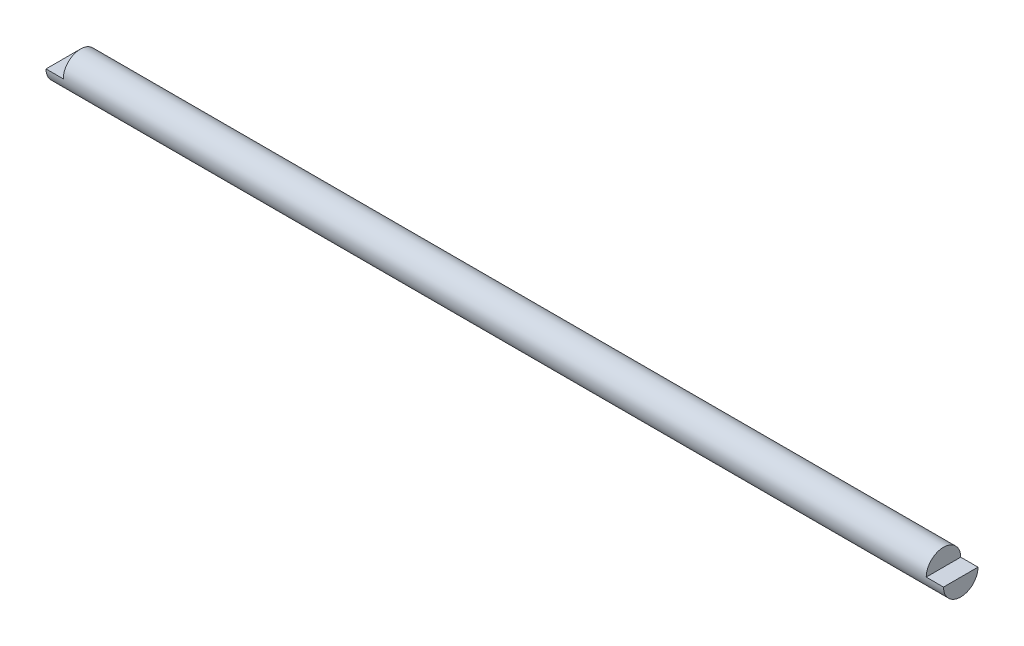
SolidWorks part; units mm, degrees
material "Cast Stainless Steel"
ref_plane "Front" through (0, 0, 0) normal (0, 0, 1) x (1, 0, 0)
ref_plane "Top" through (0, 0, 0) normal (0, 1, 0) x (1, 0, 0)
ref_plane "Right" through (0, 0, 0) normal (1, 0, 0) x (0, 0, -1)
sketch "Sketch1" plane through (0, 0, 0) normal (1, 0, 0) x (0, 0, -1)
  circle A0 centre (0, 0) radius 6.35
  dimension "D1" = 12.7
extrude "Boss-Extrude1" add sketch "Sketch1" along normal blind 330.2
sketch "Sketch2" plane through (0, 0, 0) normal (0, 0, 1) x (1, 0, 0)
  line L0 (330.2, 6.35) -> (0, 6.35) construction
  line L1 (0, 0) -> (6.35, 0)
  line L2 (0, 0) -> (0, 6.35)
  line L3 (0, 6.35) -> (6.35, 6.35)
  line L4 (6.35, 0) -> (6.35, 6.35)
  line L5 (165.1, 6.35) -> (165.1, 50006.35) construction
  line L6 (330.2, 0) -> (323.85, 0)
  line L7 (330.2, 0) -> (330.2, 6.35)
  line L8 (330.2, 6.35) -> (323.85, 6.35)
  line L9 (323.85, 0) -> (323.85, 6.35)
  point P9 (165.1, 6.35)
  dimension "D1" = 6.35
extrude "Cut-Extrude1" cut sketch "Sketch2" against normal through all and the other way through all
